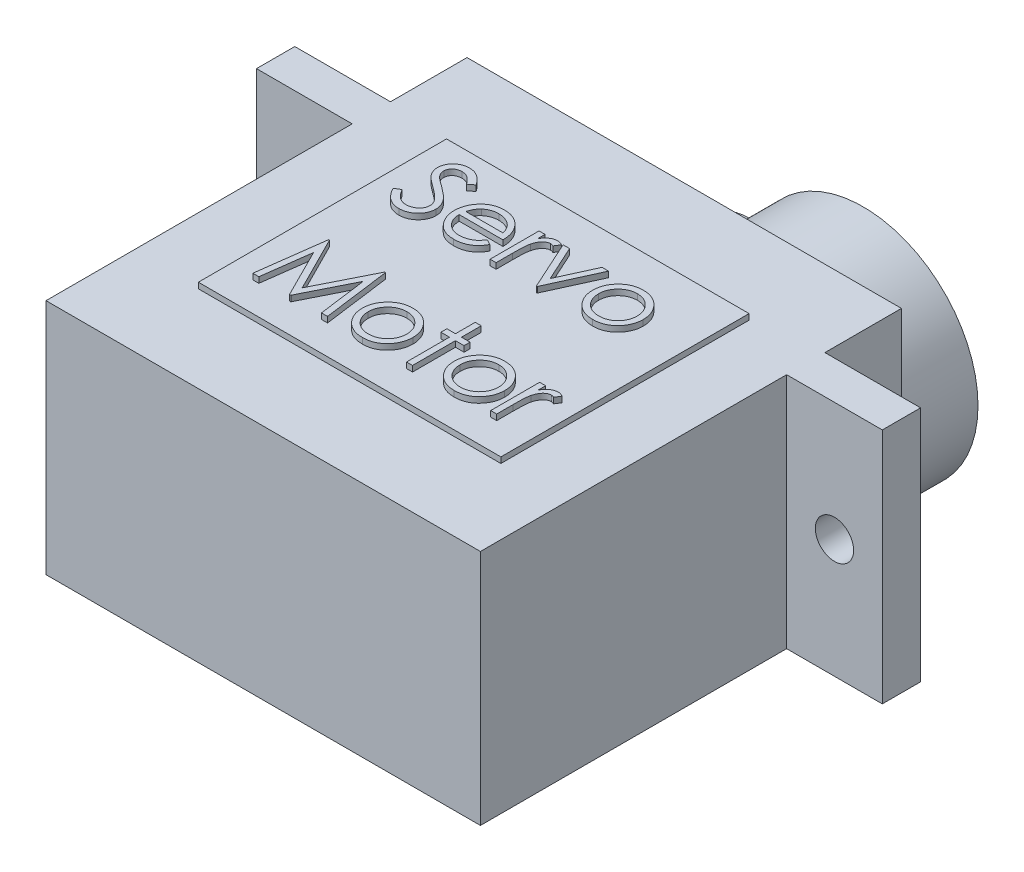
SolidWorks part; units mm, degrees
ref_plane "Front Plane" through (0, 0, 0) normal (0, 0, 1) x (1, 0, 0)
ref_plane "Top Plane" through (0, 0, 0) normal (0, 1, 0) x (1, 0, 0)
ref_plane "Right Plane" through (0, 0, 0) normal (1, 0, 0) x (0, 0, -1)
sketch "Sketch1" plane through (0, 0, 0) normal (0, 1, 0) x (1, 0, 0)
  line L0 (-11.35, 5) -> (-11.35, -11)
  line L1 (-11.35, 11) -> (11.35, 11)
  line L2 (-11.35, 11) -> (-11.35, 7)
  line L3 (-11.35, -11) -> (11.35, -11)
  line L4 (11.35, 11) -> (11.35, 7)
  line L5 (-11.35, 11) -> (11.35, -11) construction
  line L6 (-11.35, -11) -> (11.35, 11) construction
  line L7 (11.35, 7) -> (16.35, 7)
  line L9 (11.35, 5) -> (16.35, 5)
  line L10 (16.35, 7) -> (16.35, 5)
  line L11 (-11.35, 7) -> (-16.35, 7)
  line L12 (11.35, 5) -> (11.35, -11)
  line L13 (-11.35, 5) -> (-16.35, 5)
  line L14 (-16.35, 7) -> (-16.35, 5)
  point P0 (0, 0)
  dimension "D1" = 22
  dimension "D2" = 22.7
  dimension "D3" = 4
  dimension "D4" = 2
  dimension "D5" = 5
  dimension "D6" = 4
  dimension "D7" = 2
  dimension "D8" = 5
extrude "Boss-Extrude1" add sketch "Sketch1" along normal blind 12.4
sketch "Sketch2" plane through (0, 0, -11) normal (0, 0, -1) x (-1, 0, 0)
  line L0 (-11.35, 12.4) -> (-11.35, 0) construction
  line L1 (-11.35, 0) -> (11.35, 0) construction
  line L2 (0.65, 8.5) -> (0.1044, 8.5)
  line L4 (0.1044, 3.5) -> (0.65, 3.5)
  arc A0 (0.1044, 8.5) -> (0.1044, 3.5) centre (-5.35, 6) ccw
  arc A1 (0.65, 3.5) -> (0.65, 8.5) centre (0.65, 6) ccw
  dimension "D1" = 6
  dimension "D2" = 6
  dimension "D3" = 12
  dimension "D4" = 5
extrude "Boss-Extrude2" add sketch "Sketch2" along normal blind 4
sketch "Sketch3" plane through (0, 12.4, 0) normal (0, 1, 0) x (1, 0, 0)
  line L1 (-7.9041, -6.4842) -> (7.9041, -6.4842)
  line L2 (-7.9041, -6.4842) -> (-7.9041, 6.4842)
  line L3 (-7.9041, 6.4842) -> (7.9041, 6.4842)
  line L4 (7.9041, -6.4842) -> (7.9041, 6.4842)
  line L5 (-7.9041, -6.4842) -> (7.9041, 6.4842) construction
  line L6 (-7.9041, 6.4842) -> (7.9041, -6.4842) construction
  point P0 (0, 0)
extrude "Boss-Extrude3" add sketch "Sketch3" along normal blind 0.3
sketch "Sketch4" plane through (0, 12.7, 0) normal (0, 1, 0) x (1, 0, 0)
  text T0 "Servo\r\nMotor"
extrude "Boss-Extrude4" add sketch "Sketch4" along normal blind 0.3
sketch "Sketch5" plane through (0, 0, -15) normal (0, 0, -1) x (-1, 0, 0)
  circle A0 centre (-5.35, 6) radius 2.5
  dimension "D1" = 5
extrude "Boss-Extrude5" add sketch "Sketch5" along normal blind 2
sketch "Sketch8" plane through (0, 0, -7) normal (0, 0, -1) x (-1, 0, 0)
  line L0 (-16.35, 12.4) -> (-11.35, 12.4) construction
  line L1 (-16.35, 12.4) -> (-16.35, 0) construction
  line L2 (11.35, 12.4) -> (16.35, 12.4) construction
  line L3 (16.35, 12.4) -> (16.35, 0) construction
  circle A0 centre (-13.85, 6.2) radius 1
  circle A1 centre (13.85, 6.2) radius 1
  dimension "D1" = 2
  dimension "D4" = 2
  dimension "D6" = 2.5
  dimension "D2" = 6.2
  dimension "D3" = 2.5
  dimension "D5" = 6.2
extrude "Cut-Extrude2" cut sketch "Sketch8" against normal up to next
